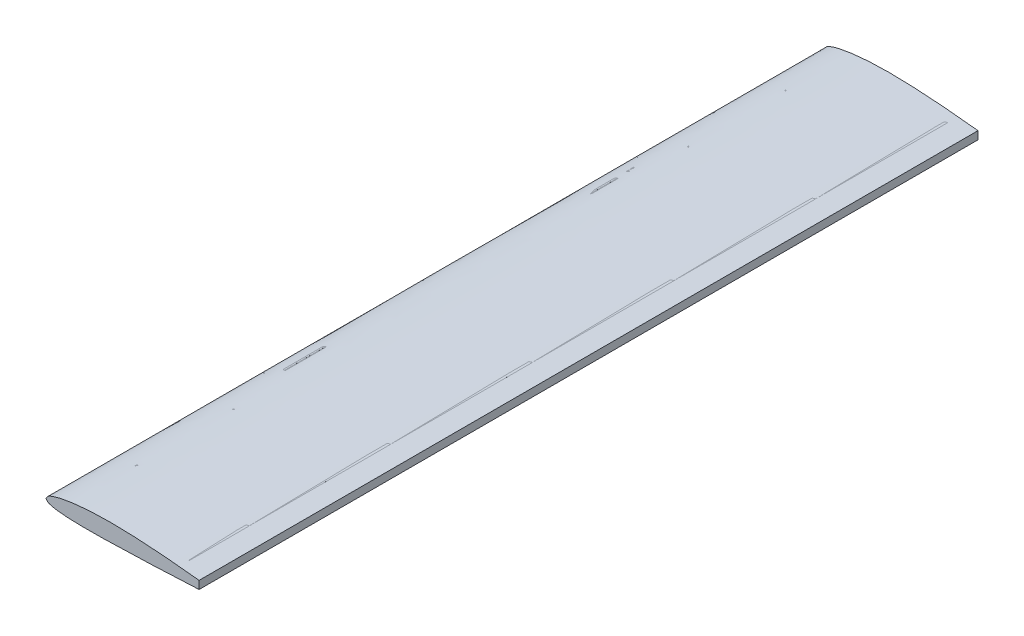
SolidWorks part; units mm, degrees
material "2024-T4"
ref_plane "Front Plane" through (0, 0, 0) normal (0, 0, 1) x (1, 0, 0)
ref_plane "Top Plane" through (0, 0, 0) normal (0, 1, 0) x (1, 0, 0)
ref_plane "Right Plane" through (0, 0, 0) normal (1, 0, 0) x (0, 0, -1)
curve "Top"
  spline degree 3 poles (0, 0, 0) (3.9101, 6.7289, 0) (10.5058, 18.0795, 0) (27.0112, 25.6481, 0) (40.59, 31.5719, 0) (54.3011, 36.3192, 0) (67.915, 40.4922, 0) (81.5319, 44.1857, 0) (95.1379, 47.5159, 0) (108.7414, 50.5421, 0) (122.3424, 53.3102, 0) (135.9422, 55.8531, 0) (149.541, 58.1958, 0) (163.1392, 60.3581, 0) (176.737, 62.3558, 0) (190.3344, 64.202, 0) (203.9316, 65.9075, 0) (217.5286, 67.4816, 0) (231.1254, 68.9321, 0) (244.7221, 70.2661, 0) (258.3187, 71.4894, 0) (271.9153, 72.6074, 0) (285.5117, 73.625, 0) (299.1081, 74.5462, 0) (312.7045, 75.3751, 0) (326.3008, 76.1151, 0) (339.8971, 76.7695, 0) (353.4934, 77.341, 0) (367.0896, 77.8326, 0) (380.6858, 78.2467, 0) (394.282, 78.5855, 0) (407.8782, 78.8514, 0) (421.4743, 79.0463, 0) (435.0705, 79.172, 0) (448.6666, 79.2305, 0) (462.2627, 79.2233, 0) (475.8588, 79.1521, 0) (489.4549, 79.0183, 0) (503.051, 78.8233, 0) (516.6471, 78.5684, 0) (530.2431, 78.2555, 0) (543.839, 77.8832, 0) (557.435, 77.469, 0) (571.031, 77.0139, 0) (584.627, 76.5188, 0) (598.223, 75.9847, 0) (611.819, 75.4126, 0) (625.415, 74.8034, 0) (639.011, 74.1578, 0) (652.607, 73.4767, 0) (666.2029, 72.761, 0) (679.7989, 72.0111, 0) (693.3949, 71.228, 0) (706.9909, 70.4122, 0) (720.5869, 69.5644, 0) (734.1828, 68.6851, 0) (747.7788, 67.7749, 0) (761.3748, 66.8344, 0) (774.9708, 65.864, 0) (788.5667, 64.8643, 0) (802.1627, 63.8356, 0) (815.7587, 62.7784, 0) (829.3546, 61.6931, 0) (842.9506, 60.58, 0) (856.5466, 59.4396, 0) (870.1426, 58.2721, 0) (883.7385, 57.0778, 0) (897.3345, 55.8569, 0) (910.9305, 54.6099, 0) (924.5265, 53.3368, 0) (938.1224, 52.0379, 0) (951.7184, 50.7134, 0) (965.3144, 49.3633, 0) (978.9104, 47.988, 0) (992.5063, 46.5875, 0) (1006.1023, 45.1619, 0) (1019.6983, 43.7112, 0) (1033.2943, 42.2356, 0) (1046.8903, 40.7351, 0) (1060.4862, 39.2096, 0) (1074.0822, 37.6593, 0) (1087.6782, 36.0841, 0) (1101.2742, 34.4839, 0) (1114.8702, 32.8588, 0) (1128.4662, 31.2085, 0) (1142.0622, 29.5331, 0) (1155.6581, 27.8325, 0) (1169.2541, 26.1064, 0) (1182.8501, 24.3548, 0) (1196.4461, 22.5774, 0) (1210.0421, 20.7742, 0) (1223.6381, 18.9448, 0) (1237.2341, 17.0892, 0) (1250.8301, 15.207, 0) (1264.4261, 13.2979, 0) (1278.0221, 11.3619, 0) (1291.6181, 9.3984, 0) (1305.2142, 7.4073, 0) (1318.8101, 5.3878, 0) (1332.4064, 3.3419, 0) (1341.4683, 1.954, 0) (1346, 1.26, 0) knots 0 0 0 0 0.016572 0.027954 0.03876 0.049312 0.059718 0.070028 0.080271 0.090463 0.100615 0.110735 0.12083 0.130902 0.140957 0.150996 0.161021 0.171035 0.181039 0.191035 0.201022 0.211003 0.220979 0.230949 0.240915 0.250877 0.260836 0.270792 0.280746 0.290699 0.300649 0.310598 0.320547 0.330495 0.340442 0.35039 0.360338 0.370286 0.380234 0.390183 0.400133 0.410084 0.420037 0.42999 0.439944 0.449899 0.459855 0.469813 0.479771 0.489731 0.499692 0.509655 0.519619 0.529584 0.539551 0.549519 0.559489 0.56946 0.579433 0.589407 0.599383 0.609361 0.61934 0.629321 0.639303 0.649287 0.659273 0.66926 0.67925 0.689241 0.699233 0.709228 0.719224 0.729223 0.739223 0.749225 0.759229 0.769235 0.779242 0.789252 0.799264 0.809278 0.819294 0.829313 0.839333 0.849356 0.859381 0.869408 0.879438 0.88947 0.899505 0.909542 0.919581 0.929624 0.939669 0.949717 0.959767 0.969821 0.979878 0.989937 1 1 1 1
curve "Bot"
  spline degree 3 poles (0, 0, 0) (3.9391, -6.157, 0) (10.6258, -16.6087, 0) (27.1033, -21.7439, 0) (40.6414, -25.7752, 0) (54.341, -28.6555, 0) (67.9447, -31.0337, 0) (81.556, -32.9828, 0) (95.1576, -34.6222, 0) (108.758, -36.0091, 0) (122.3566, -37.1896, 0) (135.9545, -38.1961, 0) (149.5518, -39.0537, 0) (163.1487, -39.782, 0) (176.7454, -40.3968, 0) (190.3419, -40.9112, 0) (203.9383, -41.3361, 0) (217.5345, -41.6805, 0) (231.1307, -41.9525, 0) (244.7269, -42.1589, 0) (258.323, -42.3057, 0) (271.9191, -42.3982, 0) (285.5151, -42.4413, 0) (299.1111, -42.4392, 0) (312.7072, -42.3956, 0) (326.3032, -42.3143, 0) (339.8991, -42.1982, 0) (353.4951, -42.0505, 0) (367.0911, -41.8737, 0) (380.6871, -41.6705, 0) (394.283, -41.4431, 0) (407.879, -41.1937, 0) (421.4749, -40.9243, 0) (435.0709, -40.6368, 0) (448.6668, -40.3331, 0) (462.2628, -40.0147, 0) (475.8587, -39.6833, 0) (489.4547, -39.3403, 0) (503.0506, -38.9872, 0) (516.6466, -38.6254, 0) (530.2425, -38.2555, 0) (543.8386, -37.8813, 0) (557.4346, -37.4875, 0) (571.0306, -37.0754, 0) (584.6265, -36.6461, 0) (598.2225, -36.2004, 0) (611.8184, -35.7394, 0) (625.4144, -35.264, 0) (639.0103, -34.7749, 0) (652.6063, -34.2729, 0) (666.2022, -33.7589, 0) (679.7982, -33.2336, 0) (693.3941, -32.6976, 0) (706.9901, -32.1516, 0) (720.586, -31.5963, 0) (734.182, -31.0322, 0) (747.7779, -30.4598, 0) (761.3739, -29.8798, 0) (774.9698, -29.2926, 0) (788.5658, -28.6987, 0) (802.1617, -28.0986, 0) (815.7577, -27.4926, 0) (829.3536, -26.8812, 0) (842.9496, -26.2647, 0) (856.5456, -25.6434, 0) (870.1415, -25.0178, 0) (883.7375, -24.3881, 0) (897.3334, -23.7545, 0) (910.9294, -23.1174, 0) (924.5253, -22.4769, 0) (938.1213, -21.8332, 0) (951.7172, -21.1866, 0) (965.3132, -20.5372, 0) (978.9092, -19.8852, 0) (992.5051, -19.2306, 0) (1006.1011, -18.5736, 0) (1019.697, -17.9143, 0) (1033.293, -17.2526, 0) (1046.8889, -16.5888, 0) (1060.4849, -15.9227, 0) (1074.0809, -15.2544, 0) (1087.6768, -14.5838, 0) (1101.2728, -13.911, 0) (1114.8687, -13.2359, 0) (1128.4647, -12.5583, 0) (1142.0607, -11.8783, 0) (1155.6566, -11.1957, 0) (1169.2526, -10.5103, 0) (1182.8486, -9.8221, 0) (1196.4445, -9.1308, 0) (1210.0405, -8.4363, 0) (1223.6365, -7.7383, 0) (1237.2324, -7.0368, 0) (1250.8284, -6.3313, 0) (1264.4244, -5.6217, 0) (1278.0203, -4.9077, 0) (1291.6163, -4.1891, 0) (1305.2123, -3.4654, 0) (1318.8082, -2.7363, 0) (1332.4042, -2.002, 0) (1341.468, -1.5073, 0) (1346, -1.26, 0) knots 0 0 0 0 0.01554 0.02638 0.036798 0.047053 0.057224 0.067347 0.077439 0.08751 0.097567 0.107613 0.117652 0.127685 0.137714 0.14774 0.157763 0.167785 0.177806 0.187826 0.197845 0.207864 0.217882 0.227901 0.23792 0.247939 0.257958 0.267977 0.277996 0.288016 0.298036 0.308056 0.318077 0.328098 0.338119 0.34814 0.358162 0.368184 0.378206 0.388228 0.39825 0.408273 0.418296 0.428319 0.438343 0.448367 0.458391 0.468416 0.478441 0.488466 0.498492 0.508518 0.518545 0.528571 0.538598 0.548626 0.558653 0.568681 0.578709 0.588737 0.598765 0.608794 0.618823 0.628852 0.638881 0.64891 0.658939 0.668969 0.678999 0.689028 0.699058 0.709088 0.719118 0.729148 0.739179 0.749209 0.759239 0.76927 0.7793 0.789331 0.799362 0.809393 0.819424 0.829455 0.839486 0.849517 0.859548 0.869579 0.879611 0.889642 0.899674 0.909706 0.919738 0.92977 0.939802 0.949835 0.959867 0.9699 0.979933 0.989967 1 1 1 1
sketch "Sketch3" plane through (0, 0, 0) normal (0, 0, 1) x (1, 0, 0)
  line L1 (0, 0) -> (1076.8, 0) construction
  line L2 (1076.8, 37.3423) -> (1076.8, -15.1201)
  line L3 (1078.8, 39.1249) -> (1078.8, -17.024)
  line L4 (1077.8, 38.2336) -> (1077.8, -16.072) construction
  spline S0 degree 3 poles (-1345.7363, -1475.2093) (73.9863, 287.8593) (-51.0903, 2.6251) (27.1033, -21.7439) (40.6414, -25.7752) (54.341, -28.6555) (67.9447, -31.0337) (81.556, -32.9828) (95.1576, -34.6222) (108.758, -36.0091) (122.3566, -37.1896) (135.9545, -38.1961) (149.5518, -39.0537) (163.1487, -39.782) (176.7454, -40.3968) (190.3419, -40.9112) (203.9383, -41.3361) (217.5345, -41.6805) (231.1307, -41.9525) (244.7269, -42.1589) (258.323, -42.3057) (271.9191, -42.3982) (285.5151, -42.4413) (299.1111, -42.4392) (312.7072, -42.3956) (326.3032, -42.3143) (339.8991, -42.1982) (353.4951, -42.0505) (367.0911, -41.8737) (380.6871, -41.6705) (394.283, -41.4431) (407.879, -41.1937) (421.4749, -40.9243) (435.0709, -40.6368) (448.6668, -40.3331) (462.2628, -40.0147) (475.8587, -39.6833) (489.4547, -39.3403) (503.0506, -38.9872) (516.6466, -38.6254) (530.2425, -38.2555) (543.8386, -37.8813) (557.4346, -37.4875) (571.0306, -37.0754) (584.6265, -36.6461) (598.2225, -36.2004) (611.8184, -35.7394) (625.4144, -35.264) (639.0103, -34.7749) (652.6063, -34.2729) (666.2022, -33.7589) (679.7982, -33.2336) (693.3941, -32.6976) (706.9901, -32.1516) (720.586, -31.5963) (734.182, -31.0322) (747.7779, -30.4598) (761.3739, -29.8798) (774.9698, -29.2926) (788.5658, -28.6987) (802.1617, -28.0986) (815.7577, -27.4926) (829.3536, -26.8812) (842.9496, -26.2647) (856.5456, -25.6434) (870.1415, -25.0178) (883.7375, -24.3881) (897.3334, -23.7545) (910.9294, -23.1174) (924.5253, -22.4769) (938.1213, -21.8332) (951.7172, -21.1866) (965.3132, -20.5372) (978.9092, -19.8852) (992.5051, -19.2306) (1006.1011, -18.5736) (1019.697, -17.9143) (1033.293, -17.2526) (1046.8889, -16.5888) (1060.4849, -15.9227) (1074.0809, -15.2544) (1087.6768, -14.5838) (1101.2728, -13.911) (1114.8687, -13.2359) (1128.4647, -12.5583) (1142.0607, -11.8783) (1155.6566, -11.1957) (1169.2526, -10.5103) (1182.8486, -9.8221) (1196.4445, -9.1308) (1210.0405, -8.4363) (1223.6365, -7.7383) (1237.2324, -7.0368) (1250.8284, -6.3313) (1264.4244, -5.6217) (1278.0203, -4.9077) (1291.6163, -4.1891) (1305.2123, -3.4654) (1318.8082, -2.7363) (1786.1325, 22.5031) (2248.1969, 60.8937) (2777.2036, -1216.076) knots -0.137826 -0.137826 -0.137826 -0.137826 0.01554 0.02638 0.036798 0.047053 0.057224 0.067347 0.077439 0.08751 0.097567 0.107613 0.117652 0.127685 0.137714 0.14774 0.157763 0.167785 0.177806 0.187826 0.197845 0.207864 0.217882 0.227901 0.23792 0.247939 0.257958 0.267977 0.277996 0.288016 0.298036 0.308056 0.318077 0.328098 0.338119 0.34814 0.358162 0.368184 0.378206 0.388228 0.39825 0.408273 0.418296 0.428319 0.438343 0.448367 0.458391 0.468416 0.478441 0.488466 0.498492 0.508518 0.518545 0.528571 0.538598 0.548626 0.558653 0.568681 0.578709 0.588737 0.598765 0.608794 0.618823 0.628852 0.638881 0.64891 0.658939 0.668969 0.678999 0.689028 0.699058 0.709088 0.719118 0.729148 0.739179 0.749209 0.759239 0.76927 0.7793 0.789331 0.799362 0.809393 0.819424 0.829455 0.839486 0.849517 0.859548 0.869579 0.879611 0.889642 0.899674 0.909706 0.919738 0.92977 0.939802 0.949835 0.959867 0.9699 0.979933 0.989967 2.004497 2.004497 2.004497 2.004497 only from (0, 0) to (1346, -1.26) construction
  spline S1 degree 3 poles (-1478.3902, 1341.2037) (85.3471, -283.5176) (-53.2012, -11.1336) (27.0112, 25.6481) (40.59, 31.5719) (54.3011, 36.3192) (67.915, 40.4922) (81.5319, 44.1857) (95.1379, 47.5159) (108.7414, 50.5421) (122.3424, 53.3102) (135.9422, 55.8531) (149.541, 58.1958) (163.1392, 60.3581) (176.737, 62.3558) (190.3344, 64.202) (203.9316, 65.9075) (217.5286, 67.4816) (231.1254, 68.9321) (244.7221, 70.2661) (258.3187, 71.4894) (271.9153, 72.6074) (285.5117, 73.625) (299.1081, 74.5462) (312.7045, 75.3751) (326.3008, 76.1151) (339.8971, 76.7695) (353.4934, 77.341) (367.0896, 77.8326) (380.6858, 78.2467) (394.282, 78.5855) (407.8782, 78.8514) (421.4743, 79.0463) (435.0705, 79.172) (448.6666, 79.2305) (462.2627, 79.2233) (475.8588, 79.1521) (489.4549, 79.0183) (503.051, 78.8233) (516.6471, 78.5684) (530.2431, 78.2555) (543.839, 77.8832) (557.435, 77.469) (571.031, 77.0139) (584.627, 76.5188) (598.223, 75.9847) (611.819, 75.4126) (625.415, 74.8034) (639.011, 74.1578) (652.607, 73.4767) (666.2029, 72.761) (679.7989, 72.0111) (693.3949, 71.228) (706.9909, 70.4122) (720.5869, 69.5644) (734.1828, 68.6851) (747.7788, 67.7749) (761.3748, 66.8344) (774.9708, 65.864) (788.5667, 64.8643) (802.1627, 63.8356) (815.7587, 62.7784) (829.3546, 61.6931) (842.9506, 60.58) (856.5466, 59.4396) (870.1426, 58.2721) (883.7385, 57.0778) (897.3345, 55.8569) (910.9305, 54.6099) (924.5265, 53.3368) (938.1224, 52.0379) (951.7184, 50.7134) (965.3144, 49.3633) (978.9104, 47.988) (992.5063, 46.5875) (1006.1023, 45.1619) (1019.6983, 43.7112) (1033.2943, 42.2356) (1046.8903, 40.7351) (1060.4862, 39.2096) (1074.0822, 37.6593) (1087.6782, 36.0841) (1101.2742, 34.4839) (1114.8702, 32.8588) (1128.4662, 31.2085) (1142.0622, 29.5331) (1155.6581, 27.8325) (1169.2541, 26.1064) (1182.8501, 24.3548) (1196.4461, 22.5774) (1210.0421, 20.7742) (1223.6381, 18.9448) (1237.2341, 17.0892) (1250.8301, 15.207) (1264.4261, 13.2979) (1278.0221, 11.3619) (1291.6181, 9.3984) (1305.2142, 7.4073) (1318.8101, 5.3878) (1630.3994, -41.4976) (1933.3109, -114.9683) (2496.3588, 1552.4265) knots -0.149606 -0.149606 -0.149606 -0.149606 0.016572 0.027954 0.03876 0.049312 0.059718 0.070028 0.080271 0.090463 0.100615 0.110735 0.12083 0.130902 0.140957 0.150996 0.161021 0.171035 0.181039 0.191035 0.201022 0.211003 0.220979 0.230949 0.240915 0.250877 0.260836 0.270792 0.280746 0.290699 0.300649 0.310598 0.320547 0.330495 0.340442 0.35039 0.360338 0.370286 0.380234 0.390183 0.400133 0.410084 0.420037 0.42999 0.439944 0.449899 0.459855 0.469813 0.479771 0.489731 0.499692 0.509655 0.519619 0.529584 0.539551 0.549519 0.559489 0.56946 0.579433 0.589407 0.599383 0.609361 0.61934 0.629321 0.639303 0.649287 0.659273 0.66926 0.67925 0.689241 0.699233 0.709228 0.719224 0.729223 0.739223 0.749225 0.759229 0.769235 0.779242 0.789252 0.799264 0.809278 0.819294 0.829313 0.839333 0.849356 0.859381 0.869408 0.879438 0.88947 0.899505 0.909542 0.919581 0.929624 0.939669 0.949717 0.959767 0.969821 0.979878 0.989937 1.661442 1.661442 1.661442 1.661442 only from (0, 0) to (1346, 1.26) construction
  spline S2 degree 3 poles (0, 0) (3.9391, -6.157) (10.6258, -16.6087) (27.1033, -21.7439) (40.6414, -25.7752) (54.341, -28.6555) (67.9447, -31.0337) (81.556, -32.9828) (95.1576, -34.6222) (108.758, -36.0091) (122.3566, -37.1896) (135.9545, -38.1961) (149.5518, -39.0537) (163.1487, -39.782) (176.7454, -40.3968) (190.3419, -40.9112) (203.9383, -41.3361) (217.5345, -41.6805) (231.1307, -41.9525) (244.7269, -42.1589) (258.323, -42.3057) (271.9191, -42.3982) (285.5151, -42.4413) (299.1111, -42.4392) (312.7072, -42.3956) (326.3032, -42.3143) (339.8991, -42.1982) (353.4951, -42.0505) (367.0911, -41.8737) (380.6871, -41.6705) (394.283, -41.4431) (407.879, -41.1937) (421.4749, -40.9243) (435.0709, -40.6368) (448.6668, -40.3331) (462.2628, -40.0147) (475.8587, -39.6833) (489.4547, -39.3403) (503.0506, -38.9872) (516.6466, -38.6254) (530.2425, -38.2555) (543.8386, -37.8813) (557.4346, -37.4875) (571.0306, -37.0754) (584.6265, -36.6461) (598.2225, -36.2004) (611.8184, -35.7394) (625.4144, -35.264) (639.0103, -34.7749) (652.6063, -34.2729) (666.2022, -33.7589) (679.7982, -33.2336) (693.3941, -32.6976) (706.9901, -32.1516) (720.586, -31.5963) (734.182, -31.0322) (747.7779, -30.4598) (761.3739, -29.8798) (774.9698, -29.2926) (788.5658, -28.6987) (802.1617, -28.0986) (815.7577, -27.4926) (829.3536, -26.8812) (842.9496, -26.2647) (856.5456, -25.6434) (870.1415, -25.0178) (883.7375, -24.3881) (897.3334, -23.7545) (910.9294, -23.1174) (924.5253, -22.4769) (938.1213, -21.8332) (951.7172, -21.1866) (965.3132, -20.5372) (978.9092, -19.8852) (992.5051, -19.2306) (1006.1011, -18.5736) (1019.697, -17.9143) (1033.293, -17.2526) (1046.8889, -16.5888) (1060.4849, -15.9227) (1070.4552, -15.4326) (1075.8936, -15.1647) (1076.8, -15.1201) knots 0 0 0 0 0.01554 0.02638 0.036798 0.047053 0.057224 0.067347 0.077439 0.08751 0.097567 0.107613 0.117652 0.127685 0.137714 0.14774 0.157763 0.167785 0.177806 0.187826 0.197845 0.207864 0.217882 0.227901 0.23792 0.247939 0.257958 0.267977 0.277996 0.288016 0.298036 0.308056 0.318077 0.328098 0.338119 0.34814 0.358162 0.368184 0.378206 0.388228 0.39825 0.408273 0.418296 0.428319 0.438343 0.448367 0.458391 0.468416 0.478441 0.488466 0.498492 0.508518 0.518545 0.528571 0.538598 0.548626 0.558653 0.568681 0.578709 0.588737 0.598765 0.608794 0.618823 0.628852 0.638881 0.64891 0.658939 0.668969 0.678999 0.689028 0.699058 0.709088 0.719118 0.729148 0.739179 0.749209 0.759239 0.76927 0.7793 0.789331 0.799362 0.801368 0.801368 0.801368 0.801368
  spline S3 degree 3 poles (0, 0) (3.9101, 6.7289) (10.5058, 18.0795) (27.0112, 25.6481) (40.59, 31.5719) (54.3011, 36.3192) (67.915, 40.4922) (81.5319, 44.1857) (95.1379, 47.5159) (108.7414, 50.5421) (122.3424, 53.3102) (135.9422, 55.8531) (149.541, 58.1958) (163.1392, 60.3581) (176.737, 62.3558) (190.3344, 64.202) (203.9316, 65.9075) (217.5286, 67.4816) (231.1254, 68.9321) (244.7221, 70.2661) (258.3187, 71.4894) (271.9153, 72.6074) (285.5117, 73.625) (299.1081, 74.5462) (312.7045, 75.3751) (326.3008, 76.1151) (339.8971, 76.7695) (353.4934, 77.341) (367.0896, 77.8326) (380.6858, 78.2467) (394.282, 78.5855) (407.8782, 78.8514) (421.4743, 79.0463) (435.0705, 79.172) (448.6666, 79.2305) (462.2627, 79.2233) (475.8588, 79.1521) (489.4549, 79.0183) (503.051, 78.8233) (516.6471, 78.5684) (530.2431, 78.2555) (543.839, 77.8832) (557.435, 77.469) (571.031, 77.0139) (584.627, 76.5188) (598.223, 75.9847) (611.819, 75.4126) (625.415, 74.8034) (639.011, 74.1578) (652.607, 73.4767) (666.2029, 72.761) (679.7989, 72.0111) (693.3949, 71.228) (706.9909, 70.4122) (720.5869, 69.5644) (734.1828, 68.6851) (747.7788, 67.7749) (761.3748, 66.8344) (774.9708, 65.864) (788.5667, 64.8643) (802.1627, 63.8356) (815.7587, 62.7784) (829.3546, 61.6931) (842.9506, 60.58) (856.5466, 59.4396) (870.1426, 58.2721) (883.7385, 57.0778) (897.3345, 55.8569) (910.9305, 54.6099) (924.5265, 53.3368) (938.1224, 52.0379) (951.7184, 50.7134) (965.3144, 49.3633) (978.9104, 47.988) (992.5063, 46.5875) (1006.1023, 45.1619) (1019.6983, 43.7112) (1033.2943, 42.2356) (1046.8903, 40.7351) (1060.4862, 39.2096) (1070.4558, 38.0728) (1075.8936, 37.4468) (1076.8, 37.3423) knots 0 0 0 0 0.016572 0.027954 0.03876 0.049312 0.059718 0.070028 0.080271 0.090463 0.100615 0.110735 0.12083 0.130902 0.140957 0.150996 0.161021 0.171035 0.181039 0.191035 0.201022 0.211003 0.220979 0.230949 0.240915 0.250877 0.260836 0.270792 0.280746 0.290699 0.300649 0.310598 0.320547 0.330495 0.340442 0.35039 0.360338 0.370286 0.380234 0.390183 0.400133 0.410084 0.420037 0.42999 0.439944 0.449899 0.459855 0.469813 0.479771 0.489731 0.499692 0.509655 0.519619 0.529584 0.539551 0.549519 0.559489 0.56946 0.579433 0.589407 0.599383 0.609361 0.61934 0.629321 0.639303 0.649287 0.659273 0.66926 0.67925 0.689241 0.699233 0.709228 0.719224 0.729223 0.739223 0.749225 0.759229 0.769235 0.779242 0.789252 0.799264 0.801267 0.801267 0.801267 0.801267
  spline S4 degree 1 poles (-2.3423, -0.0501) (1078.8, 39.1249) knots 0 0 1 1 construction
  spline S5 degree 1 poles (-2.3423, -0.0501) (1078.8, -17.024) knots 0 0 1 1 construction
  spline S6 degree 3 poles (-2.3423, -0.0501) (-1.6, 1.2273) (-0.1239, 3.779) (2.9437, 8.8794) (6.3349, 13.7678) (10.3862, 18.1012) (15.0404, 21.9084) (20.3074, 24.7496) (25.6582, 27.189) (30.9269, 29.5304) (37.5188, 32.3647) (45.6119, 35.4376) (53.8075, 38.2034) (62.0293, 40.7876) (73.0602, 44.0048) (86.9482, 47.6379) (103.7129, 51.5271) (120.5574, 55.0189) (137.4615, 58.1736) (160.0647, 61.9848) (188.415, 66.0912) (222.5404, 70.1483) (268.1403, 74.5554) (325.2702, 78.4122) (393.9239, 80.8747) (462.6085, 81.485) (519.8399, 80.6267) (565.595, 79.235) (611.3375, 77.5245) (668.4885, 74.7772) (737.0202, 70.6273) (828.3242, 64.0562) (942.3128, 54.07) (1033.3349, 44.3675) (1078.8, 39.1249) knots -0.000866 -0.000866 -0.000866 -0.000866 0.002272 0.005411 0.011688 0.014826 0.017965 0.024241 0.02738 0.030518 0.036795 0.043072 0.049349 0.055626 0.061903 0.074456 0.08701 0.099564 0.112117 0.124671 0.149778 0.174886 0.199993 0.250208 0.300423 0.350638 0.400853 0.42596 0.451067 0.501282 0.551497 0.601712 0.702142 0.802571 0.802571 0.802571 0.802571
  spline S7 degree 3 poles (1078.8, -17.024) (1033.4128, -19.2602) (942.6355, -23.6666) (829.1506, -28.9455) (738.3475, -32.8923) (670.2344, -35.6476) (602.1093, -38.141) (533.963, -40.2016) (465.8213, -41.9736) (397.6627, -43.4705) (329.4876, -44.4237) (272.659, -44.522) (227.1917, -43.9403) (193.0929, -43.0814) (164.6845, -41.9119) (141.9695, -40.6098) (124.9427, -39.4152) (107.9295, -37.9597) (90.94, -36.1793) (73.9782, -33.9994) (59.9073, -31.7048) (48.6822, -29.5247) (40.279, -27.6227) (33.4193, -25.7053) (27.9441, -24.059) (22.3993, -22.3798) (16.7474, -20.3948) (11.5704, -17.3067) (8.1835, -14.3926) (5.2058, -11.0896) (2.5272, -7.5161) (0.0413, -3.7895) (-1.5442, -1.2975) (-2.3423, -0.0501) knots -0.000865 -0.000865 -0.000865 -0.000865 0.09959 0.200044 0.250271 0.300499 0.350726 0.400953 0.45118 0.501408 0.551635 0.601862 0.626976 0.652089 0.677203 0.68976 0.702316 0.714873 0.72743 0.739987 0.752544 0.758822 0.7651 0.771379 0.774518 0.777657 0.783936 0.787075 0.790214 0.793353 0.796493 0.799632 0.802771 0.802771 0.802771 0.802771
  spline S8 degree 1 poles (-1.1711, -0.025) (1077.8, 38.2336) knots 0 0 1 1 construction
  spline S9 degree 1 poles (-1.1711, -0.025) (1077.8, -16.072) knots 0 0 1 1 construction
  spline S10 degree 3 poles (-1.1711, -0.025) (0.3089, 2.522) (3.264, 7.6454) (7.486, 13.6061) (11.4944, 17.7626) (16.0623, 21.3572) (21.2534, 24.0957) (26.5637, 26.4967) (31.8182, 28.8303) (38.3804, 31.6349) (46.4306, 34.6654) (57.3121, 38.321) (71.0086, 42.4438) (87.6283, 46.7743) (104.3469, 50.6419) (121.1496, 54.1158) (138.0139, 57.2557) (160.5662, 61.0501) (188.8564, 65.14) (222.9131, 69.1821) (268.4248, 73.5741) (325.4493, 77.4189) (393.9812, 79.8748) (462.5484, 80.4843) (519.6822, 79.6298) (565.3652, 78.2421) (611.0363, 76.5364) (668.0993, 73.7965) (736.5269, 69.6574) (827.6937, 63.1034) (941.5127, 53.1394) (1032.4023, 43.4684) (1077.8, 38.2336) knots -0.000433 -0.000433 -0.000433 -0.000433 0.005835 0.012104 0.015238 0.018372 0.02464 0.027775 0.030909 0.037177 0.043446 0.049714 0.062251 0.074787 0.087324 0.099861 0.112398 0.124934 0.150008 0.175082 0.200155 0.250302 0.300449 0.350596 0.400743 0.425817 0.45089 0.501037 0.551184 0.601331 0.701625 0.801919 0.801919 0.801919 0.801919 construction
  spline S11 degree 3 poles (1077.8, -16.072) (1032.4774, -18.3051) (941.829, -22.7036) (828.5065, -27.9735) (737.8347, -31.9129) (669.8211, -34.6627) (601.7964, -37.1509) (533.754, -39.2066) (465.7099, -40.9759) (397.654, -42.4702) (329.5847, -43.4224) (272.849, -43.5223) (227.4604, -42.9448) (193.4236, -42.0913) (165.0703, -40.9289) (142.4027, -39.6351) (125.4134, -38.4484) (108.4406, -37.0032) (91.4953, -35.2366) (74.5828, -33.0749) (60.5617, -30.8048) (49.3791, -28.6463) (41.0251, -26.7785) (34.2031, -24.8917) (28.7479, -23.2577) (23.2318, -21.5913) (17.665, -19.6851) (12.6251, -16.822) (9.2974, -14.0774) (6.3537, -10.9083) (2.8023, -6.2684) (0.4183, -2.5094) (-1.1711, -0.025) knots -0.000432 -0.000432 -0.000432 -0.000432 0.09988 0.200193 0.250349 0.300506 0.350662 0.400819 0.450975 0.501131 0.551288 0.601444 0.626522 0.6516 0.676679 0.689218 0.701757 0.714296 0.726835 0.739374 0.751913 0.758183 0.764452 0.770722 0.773856 0.776991 0.783261 0.786396 0.78953 0.792665 0.7958 0.802069 0.802069 0.802069 0.802069 construction
  point P13 (0, 0)
  point P14 (0, 0)
  point P15 (0, 0)
  dimension "D1" = 1076.8
  dimension "D2" = 2
  dimension "D3" = 1
extrude "Skin" add sketch "Sketch3" along normal blind 5500
sketch "Sketch4" plane through (0, 0, 0) normal (0, 0, 1) x (1, 0, 0)
  line L0 (273.9, 73.5931) -> (273.9, -43.3902)
  line L1 (269.9, 73.5931) -> (269.9, -43.3902)
  line L2 (1074.8, 37.5726) -> (1074.8, -15.2186)
  line L3 (1078.8, 37.5726) -> (1078.8, -15.2186)
  line L4 (1074.8, 37.5726) -> (1078.8, 37.5726)
  line L5 (1074.8, -15.2186) -> (1078.8, -15.2186)
  line L6 (273.9, 73.5931) -> (269.9, 73.5931)
  line L7 (273.9, -43.3902) -> (269.9, -43.3902)
  line L8 (271.9, 73.5931) -> (271.9, -43.3902) construction
  line L9 (1076.8, 37.5726) -> (1076.8, -15.2186) construction
  line L10 (1076.8, -15.1201) -> (1076.8, 37.3423) construction
  spline S0 degree 3 poles (1076.8, 37.3423) (1075.8936, 37.4468) (1070.4558, 38.0728) (1060.4862, 39.2096) (1046.8903, 40.7351) (1033.2943, 42.2356) (1019.6983, 43.7112) (1006.1023, 45.1619) (992.5063, 46.5875) (978.9104, 47.988) (965.3144, 49.3633) (951.7184, 50.7134) (938.1224, 52.0379) (924.5265, 53.3368) (910.9305, 54.6099) (897.3345, 55.8569) (883.7385, 57.0778) (870.1426, 58.2721) (856.5466, 59.4396) (842.9506, 60.58) (829.3546, 61.6931) (815.7587, 62.7784) (802.1627, 63.8356) (788.5667, 64.8643) (774.9708, 65.864) (761.3748, 66.8344) (747.7788, 67.7749) (734.1828, 68.6851) (720.5869, 69.5644) (706.9909, 70.4122) (693.3949, 71.228) (679.7989, 72.0111) (666.2029, 72.761) (652.607, 73.4767) (639.011, 74.1578) (625.415, 74.8034) (611.819, 75.4126) (598.223, 75.9847) (584.627, 76.5188) (571.031, 77.0139) (557.435, 77.469) (543.839, 77.8832) (530.2431, 78.2555) (516.6471, 78.5684) (503.051, 78.8233) (489.4549, 79.0183) (475.8588, 79.1521) (462.2627, 79.2233) (448.6666, 79.2305) (435.0705, 79.172) (421.4743, 79.0463) (407.8782, 78.8514) (394.282, 78.5855) (380.6858, 78.2467) (367.0896, 77.8326) (353.4934, 77.341) (339.8971, 76.7695) (326.3008, 76.1151) (312.7045, 75.3751) (299.1081, 74.5462) (285.5117, 73.625) (271.9153, 72.6074) (258.3187, 71.4894) (244.7221, 70.2661) (231.1254, 68.9321) (217.5286, 67.4816) (203.9316, 65.9075) (190.3344, 64.202) (176.737, 62.3558) (163.1392, 60.3581) (149.541, 58.1958) (135.9422, 55.8531) (122.3424, 53.3102) (108.7414, 50.5421) (95.1379, 47.5159) (81.5319, 44.1857) (67.915, 40.4922) (54.3011, 36.3192) (40.59, 31.5719) (27.0112, 25.6481) (10.5058, 18.0795) (3.9101, 6.7289) (0, 0) knots 0.198733 0.198733 0.198733 0.198733 0.200736 0.210748 0.220758 0.230765 0.240771 0.250775 0.260777 0.270777 0.280776 0.290772 0.300767 0.310759 0.32075 0.33074 0.340727 0.350713 0.360697 0.370679 0.38066 0.390639 0.400617 0.410593 0.420567 0.43054 0.440511 0.450481 0.460449 0.470416 0.480381 0.490345 0.500308 0.510269 0.520229 0.530187 0.540145 0.550101 0.560056 0.57001 0.579963 0.589916 0.599867 0.609817 0.619766 0.629714 0.639662 0.64961 0.659558 0.669505 0.679453 0.689402 0.699351 0.709301 0.719254 0.729208 0.739164 0.749123 0.759085 0.769051 0.779021 0.788997 0.798978 0.808965 0.818961 0.828965 0.838979 0.849004 0.859043 0.869098 0.87917 0.889265 0.899385 0.909537 0.919729 0.929972 0.940282 0.950688 0.96124 0.972046 0.983428 1 1 1 1 construction
  spline S1 degree 3 poles (0, 0) (3.9391, -6.157) (10.6258, -16.6087) (27.1033, -21.7439) (40.6414, -25.7752) (54.341, -28.6555) (67.9447, -31.0337) (81.556, -32.9828) (95.1576, -34.6222) (108.758, -36.0091) (122.3566, -37.1896) (135.9545, -38.1961) (149.5518, -39.0537) (163.1487, -39.782) (176.7454, -40.3968) (190.3419, -40.9112) (203.9383, -41.3361) (217.5345, -41.6805) (231.1307, -41.9525) (244.7269, -42.1589) (258.323, -42.3057) (271.9191, -42.3982) (285.5151, -42.4413) (299.1111, -42.4392) (312.7072, -42.3956) (326.3032, -42.3143) (339.8991, -42.1982) (353.4951, -42.0505) (367.0911, -41.8737) (380.6871, -41.6705) (394.283, -41.4431) (407.879, -41.1937) (421.4749, -40.9243) (435.0709, -40.6368) (448.6668, -40.3331) (462.2628, -40.0147) (475.8587, -39.6833) (489.4547, -39.3403) (503.0506, -38.9872) (516.6466, -38.6254) (530.2425, -38.2555) (543.8386, -37.8813) (557.4346, -37.4875) (571.0306, -37.0754) (584.6265, -36.6461) (598.2225, -36.2004) (611.8184, -35.7394) (625.4144, -35.264) (639.0103, -34.7749) (652.6063, -34.2729) (666.2022, -33.7589) (679.7982, -33.2336) (693.3941, -32.6976) (706.9901, -32.1516) (720.586, -31.5963) (734.182, -31.0322) (747.7779, -30.4598) (761.3739, -29.8798) (774.9698, -29.2926) (788.5658, -28.6987) (802.1617, -28.0986) (815.7577, -27.4926) (829.3536, -26.8812) (842.9496, -26.2647) (856.5456, -25.6434) (870.1415, -25.0178) (883.7375, -24.3881) (897.3334, -23.7545) (910.9294, -23.1174) (924.5253, -22.4769) (938.1213, -21.8332) (951.7172, -21.1866) (965.3132, -20.5372) (978.9092, -19.8852) (992.5051, -19.2306) (1006.1011, -18.5736) (1019.697, -17.9143) (1033.293, -17.2526) (1046.8889, -16.5888) (1060.4849, -15.9227) (1070.4552, -15.4326) (1075.8936, -15.1647) (1076.8, -15.1201) knots 0 0 0 0 0.01554 0.02638 0.036798 0.047053 0.057224 0.067347 0.077439 0.08751 0.097567 0.107613 0.117652 0.127685 0.137714 0.14774 0.157763 0.167785 0.177806 0.187826 0.197845 0.207864 0.217882 0.227901 0.23792 0.247939 0.257958 0.267977 0.277996 0.288016 0.298036 0.308056 0.318077 0.328098 0.338119 0.34814 0.358162 0.368184 0.378206 0.388228 0.39825 0.408273 0.418296 0.428319 0.438343 0.448367 0.458391 0.468416 0.478441 0.488466 0.498492 0.508518 0.518545 0.528571 0.538598 0.548626 0.558653 0.568681 0.578709 0.588737 0.598765 0.608794 0.618823 0.628852 0.638881 0.64891 0.658939 0.668969 0.678999 0.689028 0.699058 0.709088 0.719118 0.729148 0.739179 0.749209 0.759239 0.76927 0.7793 0.789331 0.799362 0.801368 0.801368 0.801368 0.801368 construction
  spline S2 degree 3 poles (-1.1711, -0.025) (0.3089, 2.522) (3.264, 7.6454) (7.486, 13.6061) (11.4944, 17.7626) (16.0623, 21.3572) (21.2534, 24.0957) (26.5637, 26.4967) (31.8182, 28.8303) (38.3804, 31.6349) (46.4306, 34.6654) (57.3121, 38.321) (71.0086, 42.4438) (87.6283, 46.7743) (104.3469, 50.6419) (121.1496, 54.1158) (138.0139, 57.2557) (160.5662, 61.0501) (188.8564, 65.14) (222.9131, 69.1821) (268.4248, 73.5741) (325.4493, 77.4189) (393.9812, 79.8748) (462.5484, 80.4843) (519.6822, 79.6298) (565.3652, 78.2421) (611.0363, 76.5364) (668.0993, 73.7965) (736.5269, 69.6574) (827.6937, 63.1034) (941.5127, 53.1394) (1032.4023, 43.4684) (1077.8, 38.2336) knots -0.000433 -0.000433 -0.000433 -0.000433 0.005835 0.012104 0.015238 0.018372 0.02464 0.027775 0.030909 0.037177 0.043446 0.049714 0.062251 0.074787 0.087324 0.099861 0.112398 0.124934 0.150008 0.175082 0.200155 0.250302 0.300449 0.350596 0.400743 0.425817 0.45089 0.501037 0.551184 0.601331 0.701625 0.801919 0.801919 0.801919 0.801919 construction
  spline S3 degree 3 poles (1077.8, -16.072) (1032.4774, -18.3051) (941.829, -22.7036) (828.5065, -27.9735) (737.8347, -31.9129) (669.8211, -34.6627) (601.7964, -37.1509) (533.754, -39.2066) (465.7099, -40.9759) (397.654, -42.4702) (329.5847, -43.4224) (272.849, -43.5223) (227.4604, -42.9448) (193.4236, -42.0913) (165.0703, -40.9289) (142.4027, -39.6351) (125.4134, -38.4484) (108.4406, -37.0032) (91.4953, -35.2366) (74.5828, -33.0749) (60.5617, -30.8048) (49.3791, -28.6463) (41.0251, -26.7785) (34.2031, -24.8917) (28.7479, -23.2577) (23.2318, -21.5913) (17.665, -19.6851) (12.6251, -16.822) (9.2974, -14.0774) (6.3537, -10.9083) (2.8023, -6.2684) (0.4183, -2.5094) (-1.1711, -0.025) knots -0.000432 -0.000432 -0.000432 -0.000432 0.09988 0.200193 0.250349 0.300506 0.350662 0.400819 0.450975 0.501131 0.551288 0.601444 0.626522 0.6516 0.676679 0.689218 0.701757 0.714296 0.726835 0.739374 0.751913 0.758183 0.764452 0.770722 0.773856 0.776991 0.783261 0.786396 0.78953 0.792665 0.7958 0.802069 0.802069 0.802069 0.802069 construction
  dimension "D1" = 4
  dimension "D2" = 271.9
  dimension "D3" = 4
extrude "Spar" add sketch "Sketch4" along normal blind 5500
sketch "Sketch5" plane through (0, 0, 0) normal (0, 0, 1) x (1, 0, 0)
  line L0 (269.9, 68.4349) -> (267.9, 68.4349)
  line L1 (269.9, 72.4313) -> (269.9, -42.3794) construction
  line L2 (267.9, 68.4349) -> (267.9, 70.112)
  line L3 (267.9, 70.112) -> (265.9, 70.112)
  line L4 (265.9, 70.112) -> (265.9, 73.112)
  line L5 (265.9, 73.112) -> (269.9, 73.4349)
  line L6 (269.9, 73.4349) -> (269.9, 68.4349)
  line L7 (273.9, 73.7491) -> (273.9, 68.7491)
  line L8 (273.9, -42.3993) -> (273.9, 72.7455) construction
  line L9 (273.9, 68.7491) -> (275.9014, 68.7491)
  line L10 (275.9014, 68.7491) -> (275.9014, 70.4262)
  line L11 (275.9014, 70.4262) -> (277.9014, 70.4262)
  line L12 (277.9014, 70.4262) -> (277.9014, 74.0547)
  line L13 (277.9014, 74.0547) -> (273.9, 73.7491)
  line L14 (273.9, 73.5931) -> (273.9, -43.3902) construction
  line L15 (269.9, 73.5931) -> (269.9, -43.3902) construction
  line L16 (269.9, -43.3796) -> (265.9, -43.3552)
  line L17 (265.9, -43.3552) -> (265.9, -40.3552)
  line L18 (265.9, -40.3552) -> (267.9, -40.3552)
  line L19 (267.9, -40.3552) -> (267.9, -38.3796)
  line L20 (267.9, -38.3796) -> (269.9, -38.3796)
  line L21 (269.9, -38.3796) -> (269.9, -43.3796)
  line L22 (273.9, -43.3997) -> (273.9, -38.3997)
  line L23 (273.9, -38.3997) -> (275.9, -38.3997)
  line L24 (275.9, -38.3997) -> (275.9, -40.4156)
  line L25 (275.9, -40.4156) -> (277.9, -40.4156)
  line L26 (277.9, -40.4156) -> (277.9, -43.4156)
  line L27 (277.9, -43.4156) -> (273.9, -43.3997)
  line L28 (1074.8, 38.5789) -> (1070.8, 39.0376)
  line L29 (1074.8, 37.5726) -> (1074.8, -15.2186) construction
  line L30 (1070.8, 39.0376) -> (1070.8, 36.0376)
  line L31 (1070.8, 36.0376) -> (1072.8, 36.0376)
  line L32 (1072.8, 36.0376) -> (1072.8, 33.5789)
  line L33 (1072.8, 33.5789) -> (1074.8, 33.5789)
  line L34 (1074.8, 33.5789) -> (1074.8, 38.5789)
  line L35 (1074.8, -16.2198) -> (1070.7787, -16.4177)
  line L36 (1070.7787, -16.4177) -> (1070.7787, -13.4177)
  line L37 (1070.7787, -13.4177) -> (1072.8, -13.4177)
  line L38 (1072.8, -13.4177) -> (1072.8, -11.2198)
  line L39 (1072.8, -11.2198) -> (1074.8, -11.2198)
  line L40 (1074.8, -11.2198) -> (1074.8, -16.2198)
  spline S4 degree 3 poles (-1.1711, -0.025) (0.3089, 2.522) (3.264, 7.6454) (7.486, 13.6061) (11.4944, 17.7626) (16.0623, 21.3572) (21.2534, 24.0957) (26.5637, 26.4967) (31.8182, 28.8303) (38.3804, 31.6349) (46.4306, 34.6654) (57.3121, 38.321) (71.0086, 42.4438) (87.6283, 46.7743) (104.3469, 50.6419) (121.1496, 54.1158) (138.0139, 57.2557) (160.5662, 61.0501) (188.8564, 65.14) (222.9131, 69.1821) (268.4248, 73.5741) (325.4493, 77.4189) (393.9812, 79.8748) (462.5484, 80.4843) (519.6822, 79.6298) (565.3652, 78.2421) (611.0363, 76.5364) (668.0993, 73.7965) (736.5269, 69.6574) (827.6937, 63.1034) (941.5127, 53.1394) (1032.4023, 43.4684) (1077.8, 38.2336) knots -0.000433 -0.000433 -0.000433 -0.000433 0.005835 0.012104 0.015238 0.018372 0.02464 0.027775 0.030909 0.037177 0.043446 0.049714 0.062251 0.074787 0.087324 0.099861 0.112398 0.124934 0.150008 0.175082 0.200155 0.250302 0.300449 0.350596 0.400743 0.425817 0.45089 0.501037 0.551184 0.601331 0.701625 0.801919 0.801919 0.801919 0.801919 construction
  spline S5 degree 3 poles (1077.8, -16.072) (1032.4774, -18.3051) (941.829, -22.7036) (828.5065, -27.9735) (737.8347, -31.9129) (669.8211, -34.6627) (601.7964, -37.1509) (533.754, -39.2066) (465.7099, -40.9759) (397.654, -42.4702) (329.5847, -43.4224) (272.849, -43.5223) (227.4604, -42.9448) (193.4236, -42.0913) (165.0703, -40.9289) (142.4027, -39.6351) (125.4134, -38.4484) (108.4406, -37.0032) (91.4953, -35.2366) (74.5828, -33.0749) (60.5617, -30.8048) (49.3791, -28.6463) (41.0251, -26.7785) (34.2031, -24.8917) (28.7479, -23.2577) (23.2318, -21.5913) (17.665, -19.6851) (12.6251, -16.822) (9.2974, -14.0774) (6.3537, -10.9083) (2.8023, -6.2684) (0.4183, -2.5094) (-1.1711, -0.025) knots -0.000432 -0.000432 -0.000432 -0.000432 0.09988 0.200193 0.250349 0.300506 0.350662 0.400819 0.450975 0.501131 0.551288 0.601444 0.626522 0.6516 0.676679 0.689218 0.701757 0.714296 0.726835 0.739374 0.751913 0.758183 0.764452 0.770722 0.773856 0.776991 0.783261 0.786396 0.78953 0.792665 0.7958 0.802069 0.802069 0.802069 0.802069 construction
  dimension "D1" = 2
  dimension "D2" = 3
  dimension "D3" = 5
  dimension "D4" = 4
  dimension "D5" = 5
  dimension "D6" = 3
  dimension "D7" = 5
  dimension "D8" = 2
  dimension "D9" = 4
  dimension "D10" = 2
  dimension "D11" = 4
  dimension "D12" = 3
extrude "SparCaps" add sketch "Sketch5" along normal blind 5500
sketch "Sketch8" plane through (0, 0, 0) normal (0, 0, 1) x (1, 0, 0)
  line L0 (25.2, 25.8773) -> (27.2, 26.7761)
  line L1 (27.2, 26.7761) -> (27.2, 22.8773)
  line L2 (27.2, 22.8773) -> (28.2, 22.8773)
  line L3 (28.2, 22.8773) -> (28.2, 21.8773)
  line L4 (28.2, 21.8773) -> (26.2, 21.8773)
  line L5 (26.2, 21.8773) -> (26.2, 23.8773)
  line L6 (26.2, 23.8773) -> (25.2, 23.8773)
  line L7 (25.2, 23.8773) -> (25.2, 25.8773)
  line L8 (106.8, 51.1061) -> (108.8, 51.5342)
  line L9 (108.8, 51.5342) -> (108.8, 48.1061)
  line L10 (108.8, 48.1061) -> (109.8, 48.1061)
  line L11 (109.8, 48.1061) -> (109.8, 47.1061)
  line L12 (109.8, 47.1061) -> (107.8, 47.1061)
  line L13 (107.8, 47.1061) -> (107.8, 49.1061)
  line L14 (107.8, 49.1061) -> (106.8, 49.1061)
  line L15 (106.8, 49.1061) -> (106.8, 51.1061)
  line L16 (188.3, 64.9199) -> (190.3, 65.1825)
  line L17 (190.3, 65.1825) -> (190.3, 61.9199)
  line L18 (190.3, 61.9199) -> (191.3, 61.9199)
  line L19 (191.3, 61.9199) -> (191.3, 60.9199)
  line L20 (191.3, 60.9199) -> (189.3, 60.9199)
  line L21 (189.3, 60.9199) -> (189.3, 62.9199)
  line L22 (189.3, 62.9199) -> (188.3, 62.9199)
  line L23 (188.3, 62.9199) -> (188.3, 64.9199)
  line L24 (27.2, -22.7887) -> (27.2, -19.1741)
  line L25 (27.2, -19.1741) -> (28.2, -19.1741)
  line L26 (28.2, -19.1741) -> (28.2, -18.1741)
  line L27 (28.2, -18.1741) -> (26.2, -18.1741)
  line L28 (26.2, -18.1741) -> (26.2, -20.1741)
  line L29 (26.2, -20.1741) -> (25.2, -20.1741)
  line L30 (25.2, -20.1741) -> (25.2, -22.1741)
  line L31 (25.2, -22.1741) -> (27.2, -22.7887)
  line L32 (108.8, -33.555) -> (108.8, -36.9831)
  line L33 (108.8, -36.9831) -> (106.8, -36.7923)
  line L34 (106.8, -36.7923) -> (106.8, -34.555)
  line L35 (106.8, -34.555) -> (107.8, -34.555)
  line L36 (107.8, -34.555) -> (107.8, -32.555)
  line L37 (107.8, -32.555) -> (109.8, -32.555)
  line L38 (109.8, -32.555) -> (109.8, -33.555)
  line L39 (109.8, -33.555) -> (108.8, -33.555)
  line L40 (190.3, -41.8955) -> (190.3, -38.8255)
  line L41 (190.3, -38.8255) -> (191.3, -38.8255)
  line L42 (191.3, -38.8255) -> (191.3, -37.8255)
  line L43 (191.3, -37.8255) -> (189.3, -37.8255)
  line L44 (189.3, -37.8255) -> (189.3, -39.8255)
  line L45 (189.3, -39.8255) -> (188.3, -39.8255)
  line L46 (188.3, -39.8255) -> (188.3, -41.8255)
  line L47 (188.3, -41.8255) -> (190.3, -41.8955)
  line L48 (365.1, 78.7532) -> (367.1, 78.8206)
  line L49 (367.1, 78.8206) -> (367.1, 75.7532)
  line L50 (367.1, 75.7532) -> (368.1, 75.7532)
  line L51 (368.1, 75.7532) -> (368.1, 74.7532)
  line L52 (368.1, 74.7532) -> (366.1, 74.7532)
  line L53 (366.1, 74.7532) -> (366.1, 76.7532)
  line L54 (366.1, 76.7532) -> (365.1, 76.7532)
  line L55 (365.1, 76.7532) -> (365.1, 78.7532)
  line L56 (555.4, 78.5292) -> (557.4, 78.4653)
  line L57 (557.4, 78.4653) -> (557.4, 75.5292)
  line L58 (557.4, 75.5292) -> (558.4, 75.5292)
  line L59 (558.4, 75.5292) -> (558.4, 74.5292)
  line L60 (558.4, 74.5292) -> (556.4, 74.5292)
  line L61 (556.4, 74.5292) -> (556.4, 76.5292)
  line L62 (556.4, 76.5292) -> (555.4, 76.5292)
  line L63 (555.4, 76.5292) -> (555.4, 78.5292)
  line L64 (367.1, -42.8699) -> (367.1, -39.8976)
  line L65 (367.1, -39.8976) -> (368.1, -39.8976)
  line L66 (368.1, -39.8976) -> (368.1, -38.8976)
  line L67 (368.1, -38.8976) -> (366.1, -38.8976)
  line L68 (366.1, -38.8976) -> (366.1, -40.8976)
  line L69 (366.1, -40.8976) -> (365.1, -40.8976)
  line L70 (365.1, -40.8976) -> (365.1, -42.8976)
  line L71 (365.1, -42.8976) -> (367.1, -42.8699)
  line L72 (557.4, -38.4759) -> (557.4, -35.5352)
  line L73 (557.4, -35.5352) -> (558.4, -35.5352)
  line L74 (558.4, -35.5352) -> (558.4, -34.5352)
  line L75 (558.4, -34.5352) -> (556.4, -34.5352)
  line L76 (556.4, -34.5352) -> (556.4, -36.5352)
  line L77 (556.4, -36.5352) -> (555.4, -36.5352)
  line L78 (555.4, -36.5352) -> (555.4, -38.5352)
  line L79 (555.4, -38.5352) -> (557.4, -38.4759)
  line L80 (745.8, 68.9065) -> (747.8, 68.7707)
  line L81 (747.8, 68.7707) -> (747.8, 65.9065)
  line L82 (747.8, 65.9065) -> (748.8, 65.9065)
  line L83 (748.8, 65.9065) -> (748.8, 64.9065)
  line L84 (748.8, 64.9065) -> (746.8, 64.9065)
  line L85 (746.8, 64.9065) -> (746.8, 66.9065)
  line L86 (746.8, 66.9065) -> (745.8, 66.9065)
  line L87 (745.8, 66.9065) -> (745.8, 68.9065)
  line L88 (747.8, -31.4586) -> (747.8, -28.5433)
  line L89 (747.8, -28.5433) -> (748.8, -28.5433)
  line L90 (748.8, -28.5433) -> (748.8, -27.5433)
  line L91 (748.8, -27.5433) -> (746.8, -27.5433)
  line L92 (746.8, -27.5433) -> (746.8, -29.5433)
  line L93 (746.8, -29.5433) -> (745.8, -29.5433)
  line L94 (745.8, -29.5433) -> (745.8, -31.5433)
  line L95 (745.8, -31.5433) -> (747.8, -31.4586)
  line L96 (936.1, 53.2333) -> (938.1, 53.0405)
  line L97 (938.1, 53.0405) -> (938.1, 50.2333)
  line L98 (938.1, 50.2333) -> (939.1, 50.2333)
  line L99 (939.1, 50.2333) -> (939.1, 49.2333)
  line L100 (939.1, 49.2333) -> (937.1, 49.2333)
  line L101 (937.1, 49.2333) -> (937.1, 51.2333)
  line L102 (937.1, 51.2333) -> (936.1, 51.2333)
  line L103 (936.1, 51.2333) -> (936.1, 53.2333)
  line L104 (938.1, -22.8349) -> (938.1, -19.9298)
  line L105 (938.1, -19.9298) -> (939.1, -19.9298)
  line L106 (939.1, -19.9298) -> (939.1, -18.9298)
  line L107 (939.1, -18.9298) -> (937.1, -18.9298)
  line L108 (937.1, -18.9298) -> (937.1, -20.9298)
  line L109 (937.1, -20.9298) -> (936.1, -20.9298)
  line L110 (936.1, -20.9298) -> (936.1, -22.9298)
  line L111 (936.1, -22.9298) -> (938.1, -22.8349)
  spline S0 degree 3 poles (-1.1711, -0.025) (0.3089, 2.522) (3.264, 7.6454) (7.486, 13.6061) (11.4944, 17.7626) (16.0623, 21.3572) (21.2534, 24.0957) (26.5637, 26.4967) (31.8182, 28.8303) (38.3804, 31.6349) (46.4306, 34.6654) (57.3121, 38.321) (71.0086, 42.4438) (87.6283, 46.7743) (104.3469, 50.6419) (121.1496, 54.1158) (138.0139, 57.2557) (160.5662, 61.0501) (188.8564, 65.14) (222.9131, 69.1821) (268.4248, 73.5741) (325.4493, 77.4189) (393.9812, 79.8748) (462.5484, 80.4843) (519.6822, 79.6298) (565.3652, 78.2421) (611.0363, 76.5364) (668.0993, 73.7965) (736.5269, 69.6574) (827.6937, 63.1034) (941.5127, 53.1394) (1032.4023, 43.4684) (1077.8, 38.2336) knots -0.000433 -0.000433 -0.000433 -0.000433 0.005835 0.012104 0.015238 0.018372 0.02464 0.027775 0.030909 0.037177 0.043446 0.049714 0.062251 0.074787 0.087324 0.099861 0.112398 0.124934 0.150008 0.175082 0.200155 0.250302 0.300449 0.350596 0.400743 0.425817 0.45089 0.501037 0.551184 0.601331 0.701625 0.801919 0.801919 0.801919 0.801919 construction
  spline S1 degree 3 poles (1077.8, -16.072) (1032.4774, -18.3051) (941.829, -22.7036) (828.5065, -27.9735) (737.8347, -31.9129) (669.8211, -34.6627) (601.7964, -37.1509) (533.754, -39.2066) (465.7099, -40.9759) (397.654, -42.4702) (329.5847, -43.4224) (272.849, -43.5223) (227.4604, -42.9448) (193.4236, -42.0913) (165.0703, -40.9289) (142.4027, -39.6351) (125.4134, -38.4484) (108.4406, -37.0032) (91.4953, -35.2366) (74.5828, -33.0749) (60.5617, -30.8048) (49.3791, -28.6463) (41.0251, -26.7785) (34.2031, -24.8917) (28.7479, -23.2577) (23.2318, -21.5913) (17.665, -19.6851) (12.6251, -16.822) (9.2974, -14.0774) (6.3537, -10.9083) (2.8023, -6.2684) (0.4183, -2.5094) (-1.1711, -0.025) knots -0.000432 -0.000432 -0.000432 -0.000432 0.09988 0.200193 0.250349 0.300506 0.350662 0.400819 0.450975 0.501131 0.551288 0.601444 0.626522 0.6516 0.676679 0.689218 0.701757 0.714296 0.726835 0.739374 0.751913 0.758183 0.764452 0.770722 0.773856 0.776991 0.783261 0.786396 0.78953 0.792665 0.7958 0.802069 0.802069 0.802069 0.802069 construction
  point P21 (107.8, 48.1061)
  point P33 (189.3, 61.9199)
  dimension "D1" = 1
  dimension "D2" = 2
  dimension "D3" = 1
  dimension "D4" = 2
  dimension "D5" = 1
  dimension "D6" = 27.2
  dimension "D7" = 1
  dimension "D8" = 1
  dimension "D9" = 108.8
  dimension "D10" = 190.3
  dimension "D11" = 1
  dimension "D12" = 367.1
  dimension "D13" = 1
  dimension "D14" = 557.4
  dimension "D15" = 1
  dimension "D16" = 747.8
  dimension "D17" = 1
  dimension "D18" = 938.1
extrude "Stringers" add sketch "Sketch8" along normal blind 5500
sketch "Sketch6" plane through (0, 0, 0) normal (0, 0, 1) x (1, 0, 0)
  line L0 (1077.8, 38.2336) -> (1077.8, -16.072) construction
  line L1 (1077.8, 38.2336) -> (1077.8, -16.072)
  spline S0 degree 3 poles (-1568.4097, 1236.0407) (-10.192, -169.6051) (-36.9182, -49.0843) (7.486, 13.6061) (11.4944, 17.7626) (16.0623, 21.3572) (21.2534, 24.0957) (26.5637, 26.4967) (31.8182, 28.8303) (38.3804, 31.6349) (46.4306, 34.6654) (57.3121, 38.321) (71.0086, 42.4438) (87.6283, 46.7743) (104.3469, 50.6419) (121.1496, 54.1158) (138.0139, 57.2557) (160.5662, 61.0501) (188.8564, 65.14) (222.9131, 69.1821) (268.4248, 73.5741) (325.4493, 77.4189) (393.9812, 79.8748) (462.5484, 80.4843) (519.6822, 79.6298) (565.3652, 78.2421) (611.0363, 76.5364) (668.0993, 73.7965) (736.5269, 69.6574) (827.6937, 63.1034) (1611.7693, -5.537) (2361.5071, -191.0044) (3034.1227, -370.8919) knots -0.149578 -0.149578 -0.149578 -0.149578 0.005835 0.012104 0.015238 0.018372 0.02464 0.027775 0.030909 0.037177 0.043446 0.049714 0.062251 0.074787 0.087324 0.099861 0.112398 0.124934 0.150008 0.175082 0.200155 0.250302 0.300449 0.350596 0.400743 0.425817 0.45089 0.501037 0.551184 0.601331 0.701625 2.278447 2.278447 2.278447 2.278447 only from (-1.1711, -0.025) to (1077.8, 38.2336) construction
  spline S1 degree 3 poles (-1.1711, -0.025) (0.3089, 2.522) (3.264, 7.6454) (7.486, 13.6061) (11.4944, 17.7626) (16.0623, 21.3572) (21.2534, 24.0957) (26.5637, 26.4967) (31.8182, 28.8303) (38.3804, 31.6349) (46.4306, 34.6654) (57.3121, 38.321) (71.0086, 42.4438) (87.6283, 46.7743) (104.3469, 50.6419) (121.1496, 54.1158) (138.0139, 57.2557) (160.5662, 61.0501) (188.8564, 65.14) (222.9131, 69.1821) (268.4248, 73.5741) (325.4493, 77.4189) (393.9812, 79.8748) (462.5484, 80.4843) (519.6822, 79.6298) (565.3652, 78.2421) (611.0363, 76.5364) (668.0993, 73.7965) (736.5269, 69.6574) (827.6937, 63.1034) (941.5127, 53.1394) (1032.4023, 43.4684) (1077.8, 38.2336) knots -0.000433 -0.000433 -0.000433 -0.000433 0.005835 0.012104 0.015238 0.018372 0.02464 0.027775 0.030909 0.037177 0.043446 0.049714 0.062251 0.074787 0.087324 0.099861 0.112398 0.124934 0.150008 0.175082 0.200155 0.250302 0.300449 0.350596 0.400743 0.425817 0.45089 0.501037 0.551184 0.601331 0.701625 0.801919 0.801919 0.801919 0.801919
  spline S2 degree 3 poles (3075.994, 66.7906) (2362.9949, 56.1169) (1607.4192, 8.2493) (828.5065, -27.9735) (737.8347, -31.9129) (669.8211, -34.6627) (601.7964, -37.1509) (533.754, -39.2066) (465.7099, -40.9759) (397.654, -42.4702) (329.5847, -43.4224) (272.849, -43.5223) (227.4604, -42.9448) (193.4236, -42.0913) (165.0703, -40.9289) (142.4027, -39.6351) (125.4134, -38.4484) (108.4406, -37.0032) (91.4953, -35.2366) (74.5828, -33.0749) (60.5617, -30.8048) (49.3791, -28.6463) (41.0251, -26.7785) (34.2031, -24.8917) (28.7479, -23.2577) (23.2318, -21.5913) (17.665, -19.6851) (12.6251, -16.822) (9.2974, -14.0774) (6.3537, -10.9083) (-36.1509, 44.624) (-9.5202, 167.1383) (-1418.9398, -1405.6955) knots -1.473378 -1.473378 -1.473378 -1.473378 0.09988 0.200193 0.250349 0.300506 0.350662 0.400819 0.450975 0.501131 0.551288 0.601444 0.626522 0.6516 0.676679 0.689218 0.701757 0.714296 0.726835 0.739374 0.751913 0.758183 0.764452 0.770722 0.773856 0.776991 0.783261 0.786396 0.78953 0.792665 0.7958 0.939604 0.939604 0.939604 0.939604 only from (1077.8, -16.072) to (-1.1711, -0.025) construction
  spline S3 degree 3 poles (1077.8, -16.072) (1032.4774, -18.3051) (941.829, -22.7036) (828.5065, -27.9735) (737.8347, -31.9129) (669.8211, -34.6627) (601.7964, -37.1509) (533.754, -39.2066) (465.7099, -40.9759) (397.654, -42.4702) (329.5847, -43.4224) (272.849, -43.5223) (227.4604, -42.9448) (193.4236, -42.0913) (165.0703, -40.9289) (142.4027, -39.6351) (125.4134, -38.4484) (108.4406, -37.0032) (91.4953, -35.2366) (74.5828, -33.0749) (60.5617, -30.8048) (49.3791, -28.6463) (41.0251, -26.7785) (34.2031, -24.8917) (28.7479, -23.2577) (23.2318, -21.5913) (17.665, -19.6851) (12.6251, -16.822) (9.2974, -14.0774) (6.3537, -10.9083) (2.8023, -6.2684) (0.4183, -2.5094) (-1.1711, -0.025) knots -0.000432 -0.000432 -0.000432 -0.000432 0.09988 0.200193 0.250349 0.300506 0.350662 0.400819 0.450975 0.501131 0.551288 0.601444 0.626522 0.6516 0.676679 0.689218 0.701757 0.714296 0.726835 0.739374 0.751913 0.758183 0.764452 0.770722 0.773856 0.776991 0.783261 0.786396 0.78953 0.792665 0.7958 0.802069 0.802069 0.802069 0.802069
extrude "Rib" add sketch "Sketch6" along normal blind 3
pattern_linear "LPattern1" count 6 spacing 1000 along (0, 0, 1) of "Rib"
sketch "Sketch7" plane through (0, 0, 5500) normal (0, 0, 1) x (1, 0, 0)
  line L0 (1077.8, 38.2336) -> (1077.8, -16.072) construction
  line L1 (1077.8, 38.2336) -> (1077.8, -16.072)
  spline S0 degree 3 poles (-1568.4097, 1236.0407) (-10.192, -169.6051) (-36.9182, -49.0843) (7.486, 13.6061) (11.4944, 17.7626) (16.0623, 21.3572) (21.2534, 24.0957) (26.5637, 26.4967) (31.8182, 28.8303) (38.3804, 31.6349) (46.4306, 34.6654) (57.3121, 38.321) (71.0086, 42.4438) (87.6283, 46.7743) (104.3469, 50.6419) (121.1496, 54.1158) (138.0139, 57.2557) (160.5662, 61.0501) (188.8564, 65.14) (222.9131, 69.1821) (268.4248, 73.5741) (325.4493, 77.4189) (393.9812, 79.8748) (462.5484, 80.4843) (519.6822, 79.6298) (565.3652, 78.2421) (611.0363, 76.5364) (668.0993, 73.7965) (736.5269, 69.6574) (827.6937, 63.1034) (1611.7693, -5.537) (2361.5071, -191.0044) (3034.1227, -370.8919) knots -0.149578 -0.149578 -0.149578 -0.149578 0.005835 0.012104 0.015238 0.018372 0.02464 0.027775 0.030909 0.037177 0.043446 0.049714 0.062251 0.074787 0.087324 0.099861 0.112398 0.124934 0.150008 0.175082 0.200155 0.250302 0.300449 0.350596 0.400743 0.425817 0.45089 0.501037 0.551184 0.601331 0.701625 2.278447 2.278447 2.278447 2.278447 only from (-1.1711, -0.025) to (1077.8, 38.2336) construction
  spline S1 degree 3 poles (-1.1711, -0.025) (0.3089, 2.522) (3.264, 7.6454) (7.486, 13.6061) (11.4944, 17.7626) (16.0623, 21.3572) (21.2534, 24.0957) (26.5637, 26.4967) (31.8182, 28.8303) (38.3804, 31.6349) (46.4306, 34.6654) (57.3121, 38.321) (71.0086, 42.4438) (87.6283, 46.7743) (104.3469, 50.6419) (121.1496, 54.1158) (138.0139, 57.2557) (160.5662, 61.0501) (188.8564, 65.14) (222.9131, 69.1821) (268.4248, 73.5741) (325.4493, 77.4189) (393.9812, 79.8748) (462.5484, 80.4843) (519.6822, 79.6298) (565.3652, 78.2421) (611.0363, 76.5364) (668.0993, 73.7965) (736.5269, 69.6574) (827.6937, 63.1034) (941.5127, 53.1394) (1032.4023, 43.4684) (1077.8, 38.2336) knots -0.000433 -0.000433 -0.000433 -0.000433 0.005835 0.012104 0.015238 0.018372 0.02464 0.027775 0.030909 0.037177 0.043446 0.049714 0.062251 0.074787 0.087324 0.099861 0.112398 0.124934 0.150008 0.175082 0.200155 0.250302 0.300449 0.350596 0.400743 0.425817 0.45089 0.501037 0.551184 0.601331 0.701625 0.801919 0.801919 0.801919 0.801919
  spline S2 degree 3 poles (3075.994, 66.7906) (2362.9949, 56.1169) (1607.4192, 8.2493) (828.5065, -27.9735) (737.8347, -31.9129) (669.8211, -34.6627) (601.7964, -37.1509) (533.754, -39.2066) (465.7099, -40.9759) (397.654, -42.4702) (329.5847, -43.4224) (272.849, -43.5223) (227.4604, -42.9448) (193.4236, -42.0913) (165.0703, -40.9289) (142.4027, -39.6351) (125.4134, -38.4484) (108.4406, -37.0032) (91.4953, -35.2366) (74.5828, -33.0749) (60.5617, -30.8048) (49.3791, -28.6463) (41.0251, -26.7785) (34.2031, -24.8917) (28.7479, -23.2577) (23.2318, -21.5913) (17.665, -19.6851) (12.6251, -16.822) (9.2974, -14.0774) (6.3537, -10.9083) (-36.1509, 44.624) (-9.5202, 167.1383) (-1418.9398, -1405.6955) knots -1.473378 -1.473378 -1.473378 -1.473378 0.09988 0.200193 0.250349 0.300506 0.350662 0.400819 0.450975 0.501131 0.551288 0.601444 0.626522 0.6516 0.676679 0.689218 0.701757 0.714296 0.726835 0.739374 0.751913 0.758183 0.764452 0.770722 0.773856 0.776991 0.783261 0.786396 0.78953 0.792665 0.7958 0.939604 0.939604 0.939604 0.939604 only from (1077.8, -16.072) to (-1.1711, -0.025) construction
  spline S3 degree 3 poles (1077.8, -16.072) (1032.4774, -18.3051) (941.829, -22.7036) (828.5065, -27.9735) (737.8347, -31.9129) (669.8211, -34.6627) (601.7964, -37.1509) (533.754, -39.2066) (465.7099, -40.9759) (397.654, -42.4702) (329.5847, -43.4224) (272.849, -43.5223) (227.4604, -42.9448) (193.4236, -42.0913) (165.0703, -40.9289) (142.4027, -39.6351) (125.4134, -38.4484) (108.4406, -37.0032) (91.4953, -35.2366) (74.5828, -33.0749) (60.5617, -30.8048) (49.3791, -28.6463) (41.0251, -26.7785) (34.2031, -24.8917) (28.7479, -23.2577) (23.2318, -21.5913) (17.665, -19.6851) (12.6251, -16.822) (9.2974, -14.0774) (6.3537, -10.9083) (2.8023, -6.2684) (0.4183, -2.5094) (-1.1711, -0.025) knots -0.000432 -0.000432 -0.000432 -0.000432 0.09988 0.200193 0.250349 0.300506 0.350662 0.400819 0.450975 0.501131 0.551288 0.601444 0.626522 0.6516 0.676679 0.689218 0.701757 0.714296 0.726835 0.739374 0.751913 0.758183 0.764452 0.770722 0.773856 0.776991 0.783261 0.786396 0.78953 0.792665 0.7958 0.802069 0.802069 0.802069 0.802069
extrude "WingCap" add sketch "Sketch7" against normal blind 3
